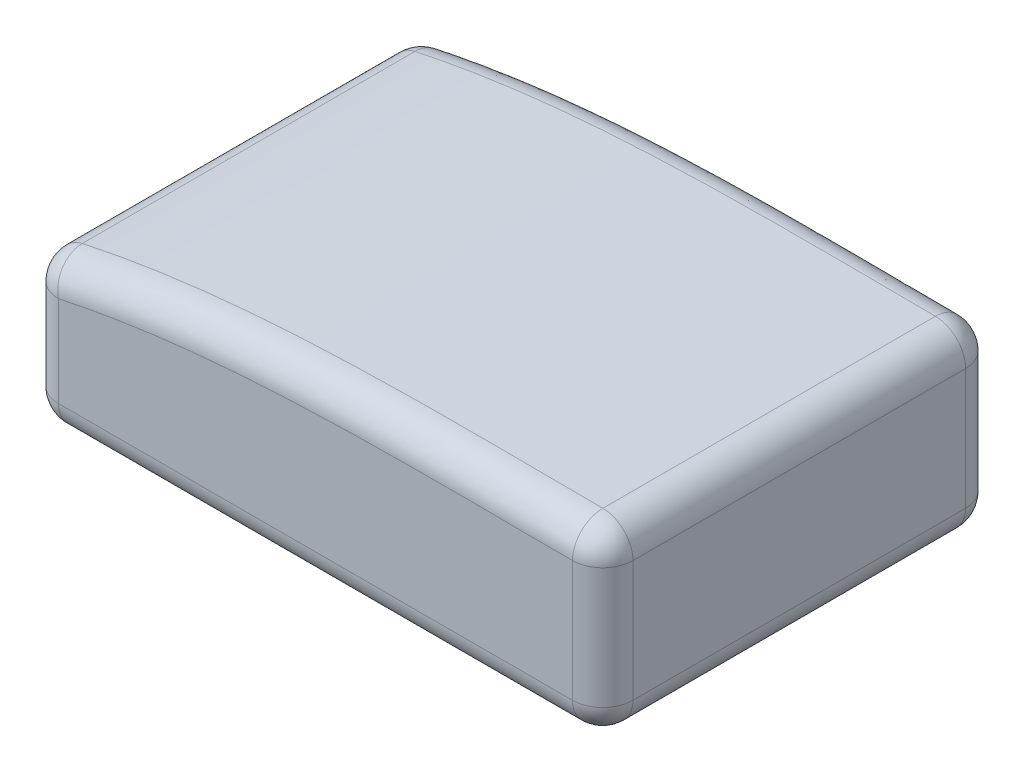
SolidWorks part; units mm, degrees
ref_plane "Front Plane" through (0, 0, 0) normal (0, 0, 1) x (1, 0, 0)
ref_plane "Top Plane" through (0, 0, 0) normal (0, 1, 0) x (1, 0, 0)
ref_plane "Right Plane" through (0, 0, 0) normal (1, 0, 0) x (0, 0, -1)
sketch "Sketch1" plane through (0, 0, 0) normal (0, 0, 1) x (1, 0, 0)
  line L0 (-47.5, 0) -> (47.5, 0) construction
  line L1 (47.5, 0) -> (47.5, 13) construction
  line L2 (-47.5, 0) -> (-47.5, 7) construction
  line L3 (-47.5, 0) -> (-47.5, -17) construction
  line L4 (47.5, 0) -> (47.5, -17) construction
  line L5 (-42.5, -17) -> (42.5, -17)
  line L6 (47.5, -12) -> (47.5, 8.0104)
  line L7 (-47.5, -12) -> (-47.5, 3.0124)
  arc A0 (42.5194, 13.0104) -> (47.5, 8.0104) centre (42.5, 8.0104) cw
  arc A1 (-43.5555, 7.8997) -> (-47.5, 3.0124) centre (-42.5, 3.0124) ccw
  arc A2 (47.5, -12) -> (42.5, -17) centre (42.5, -12) cw
  arc A3 (-47.5, -12) -> (-42.5, -17) centre (-42.5, -12) ccw
  spline S0 degree 3 poles (-43.5555, 7.8997) (-30.1767, 10.7892) (-1.3525, 13.579) (27.425, 13.0689) (42.5194, 13.0104) knots 0.042376 0.042376 0.042376 0.042376 0.472818 0.947723 0.947723 0.947723 0.947723
  dimension "D1" = 5
  dimension "D2" = 5
extrude "Boss-Extrude1" add sketch "Sketch1" along normal blind 65
fillet "Fillet1" radius 5 16 edges at (46.0424, 11.5391, 65) (47.5, -1.9948, 65) (46.0355, -15.5355, 65) (0, -17, 65) (-46.0355, -15.5355, 65) (-47.5, -4.4938, 65) (-46.3909, 6.1527, 65) (46.0424, 11.5391, 0) (47.5, -1.9948, 0) (46.0355, -15.5355, 0) (0, -17, 0) (-46.0355, -15.5355, 0) (-47.5, -4.4938, 0) (-46.3909, 6.1527, 0)
